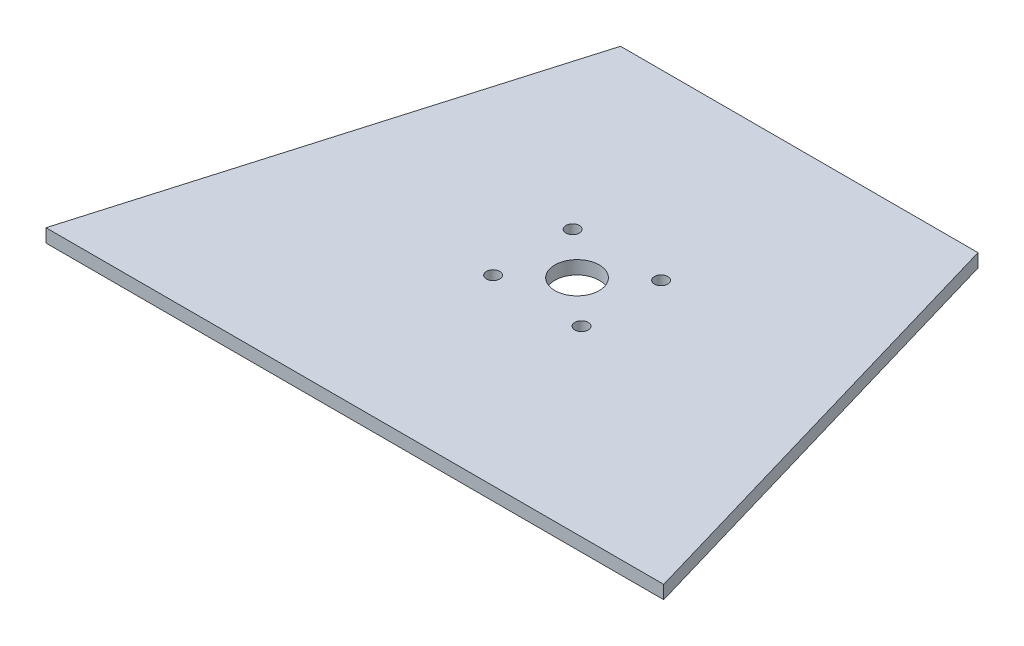
SolidWorks part; units mm, degrees
ref_plane "Front Plane" through (0, 0, 0) normal (0, 0, 1) x (1, 0, 0)
ref_plane "Top Plane" through (0, 0, 0) normal (0, 1, 0) x (1, 0, 0)
ref_plane "Right Plane" through (0, 0, 0) normal (1, 0, 0) x (0, 0, -1)
sketch "Sketch1" plane through (0, 0, 0) normal (0, 1, 0) x (1, 0, 0)
  line L0 (0, 0) -> (139, 0)
  line L1 (0, 0) -> (29.2799, 100)
  line L2 (139, 0) -> (109.7201, 100)
  line L3 (66.5, 0) -> (66.5, 100) construction
  line L4 (29.2799, 100) -> (109.7201, 100)
extrude "Boss-Extrude1" add sketch "Sketch1" along normal blind 3
hole_wizard "Ø10.0mm Dowel Hole1" positions "Sketch2" profile "Sketch3" hole size "Ø10.0" standard "ANSI Metric" end condition up to next
sketch "Sketch2" plane through (0, 0, 0) normal (0, -1, 0) x (-1, 0, 0)
  point P0 (-69.5, 50)
sketch "Sketch3" plane through (69.5, 0, -50) normal (1, 0, 0) x (0, 0, -1)
  line L0 (0, 0) -> (0, 3)
  line L1 (0, 3) -> (5, 3)
  line L2 (5, 3) -> (5, 0)
  line L5 (5, 0) -> (0, 0)
  line L11 (0, -6.35) -> (0, 107.95) construction
  dimension "Thru Hole Dia." = 10
  dimension "Thru Hole Depth" = 3
hole_wizard "Ø3.0mm Dowel Hole1" positions "Sketch4" profile "Sketch5" hole size "Ø3.0" standard "ANSI Metric" end condition up to next
sketch "Sketch4" plane through (0, 0, 0) normal (0, -1, 0) x (-1, 0, 0)
  point P0 (-59.55, 41.05)
  point P3 (-79.45, 41.05)
  point P6 (-79.45, 58.95)
  point P9 (-59.55, 58.95)
sketch "Sketch5" plane through (59.55, 0, -41.05) normal (1, 0, 0) x (0, 0, -1)
  line L0 (0, 0) -> (0, 3)
  line L1 (0, 3) -> (1.5, 3)
  line L2 (1.5, 3) -> (1.5, 0)
  line L5 (1.5, 0) -> (0, 0)
  line L11 (0, -6.35) -> (0, 107.95) construction
  dimension "Thru Hole Dia." = 3
  dimension "Thru Hole Depth" = 3
